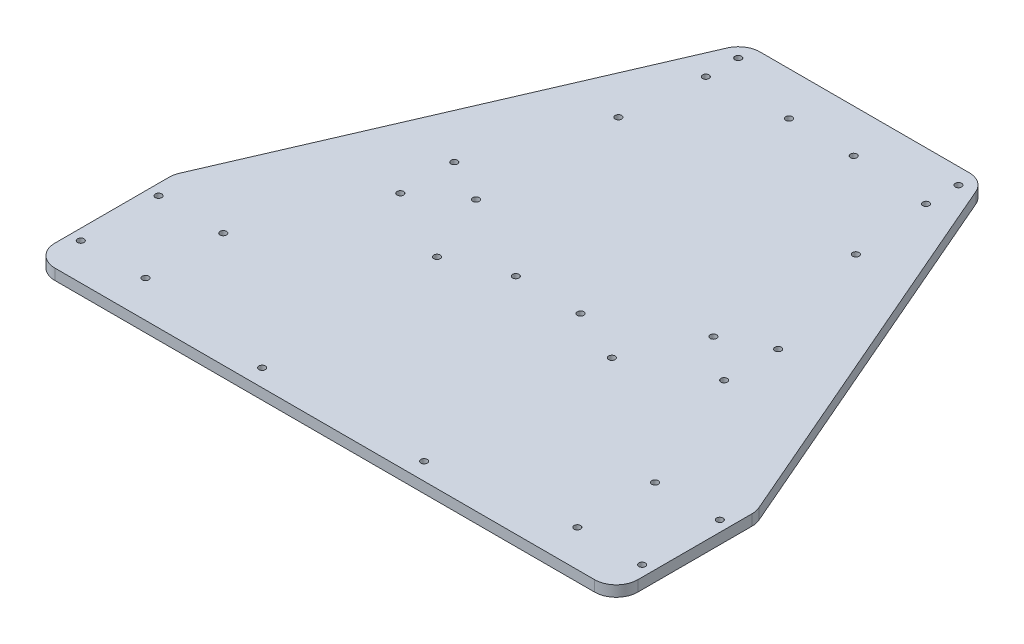
SolidWorks part; units mm, degrees
material "西洋杉"
ref_plane "正面" through (0, 0, 0) normal (0, 0, 1) x (1, 0, 0)
ref_plane "平面" through (0, 0, 0) normal (0, 1, 0) x (1, 0, 0)
ref_plane "右側面" through (0, 0, 0) normal (1, 0, 0) x (0, 0, -1)
sketch "ｽｹｯﾁ1" plane through (0, 0, 0) normal (0, 1, 0) x (1, 0, 0)
  line L0 (55, 125) -> (135, -60)
  line L1 (-135, -125) -> (135, -125)
  line L2 (-135, -125) -> (-135, 125)
  line L3 (-135, 125) -> (135, 125)
  line L4 (135, -125) -> (135, 125)
  line L5 (-135, -125) -> (135, 125) construction
  line L6 (-135, 125) -> (135, -125) construction
  line L7 (-55, 125) -> (-135, -60)
  point P0 (0, 0)
  dimension "D1" = 270
  dimension "D2" = 250
  dimension "D3" = 80
  dimension "D4" = 80
  dimension "D5" = 185
  dimension "D6" = 185
extrude "シャーシ形成" add sketch "ｽｹｯﾁ1" along normal blind 5 contours L3 L7 L2 L1 L4 L0
sketch "ｽｹｯﾁ2" plane through (0, 0, 0) normal (0, -1, 0) x (1, 0, 0)
  line L0 (130, 90) -> (130, 108)
  line L1 (-135, 90) -> (152.5185, 90)
  line L2 (-135, 125) -> (-135, 60) construction
  line L3 (-135, 125) -> (135, 125) construction
  line L4 (135, 125) -> (135, 60) construction
  line L5 (-130, 90) -> (-130, 72)
  line L6 (-130, 90) -> (-130, 108)
  line L7 (130, 90) -> (130, 72)
  circle A0 centre (-130, 90) radius 1.5
  circle A1 centre (130, 90) radius 1.5
  circle A2 centre (-130, 72) radius 1.5
  circle A3 centre (-130, 108) radius 1.5
  circle A4 centre (130, 72) radius 1.5
  circle A5 centre (130, 108) radius 1.5
  dimension "D4" = 3
  dimension "D5" = 3
  dimension "D10" = 3
  dimension "D11" = 3
  dimension "D12" = 3
  dimension "D13" = 3
  dimension "D1" = 35
  dimension "D2" = 5
  dimension "D3" = 5
  dimension "D6" = 18
  dimension "D7" = 18
  dimension "D8" = 18
  dimension "D9" = 18
extrude "外側モータマウンタ穴" cut sketch "ｽｹｯﾁ2" against normal through all contours A2 | A3 | A4 | A5
fillet "角ﾌｨﾚｯﾄ" radius 10 6 edges at (135, 2.5, 60) (135, 2.5, 125) (-135, 2.5, 125) (-135, 2.5, 60) (-55, 2.5, -125) (55, 2.5, -125)
sketch "ｽｹｯﾁ9" plane through (0, 0, 0) normal (0, -1, 0) x (1, 0, 0)
  line L0 (0, -125) -> (0, -105)
  line L1 (-48.4294, -125) -> (48.4294, -125) construction
  line L2 (0, -105) -> (15, -105)
  line L3 (15, -105) -> (-15, -105)
  circle A0 centre (15, -105) radius 1.5
  circle A1 centre (-15, -105) radius 1.5
  dimension "D4" = 3
  dimension "D5" = 3
  dimension "D1" = 20
  dimension "D2" = 15
  dimension "D3" = 30
extrude "キャスター穴" cut sketch "ｽｹｯﾁ9" against normal blind 5 contours A0 | A1
ref_plane "平面1" through (-134.1786, 5, 58.1004) normal (-0.3969, 0, 0.9179) x (0.9179, 0, 0.3969)
ref_plane "平面2" through (0, 5, 0) normal (0, -1, 0) x (-1, 0, 0)
sketch "ｽｹｯﾁ35" plane through (0, 0, 0) normal (0, -1, 0) x (1, 0, 0)
  line L0 (-48.4294, -125) -> (48.4294, -125) construction
  line L1 (0, -125) -> (50, -125)
  line L2 (0, -125) -> (0, 21.5)
  line L3 (0, 21.5) -> (50, 21.5)
  line L4 (50, -125) -> (50, 21.5)
  line L6 (0, -125) -> (-50, -125)
  line L7 (0, -125) -> (0, 21.5)
  line L8 (0, 21.5) -> (-50, 21.5)
  line L9 (-50, -125) -> (-50, 21.5)
  circle A1 centre (-15, 21.5) radius 1.5
  circle A2 centre (15, 21.5) radius 1.5
  dimension "D5" = 3
  dimension "D6" = 3
  dimension "D1" = 50
  dimension "D2" = 50
  dimension "D3" = 146.5
  dimension "D9" = 15
  dimension "D10" = 15
extrude "バッテリー固定棒の穴" cut sketch "ｽｹｯﾁ35" against normal blind 5
sketch "ｽｹｯﾁ38" plane through (0, 0, 0) normal (0, -1, 0) x (1, 0, 0)
  circle A0 centre (-100, 72) radius 1.5
  circle A1 centre (-100, 108) radius 1.5
  circle A2 centre (-130, 108) radius 1.5 construction
  circle A3 centre (-130, 72) radius 1.5 construction
  dimension "D3" = 3
  dimension "D4" = 3
  dimension "D6" = 30
  dimension "D8" = 36
  dimension "D5" = 30
  dimension "D7" = 0
extrude "内側モータマウンタ穴1" cut sketch "ｽｹｯﾁ38" against normal blind 5 contours A0 | A1
sketch "ｽｹｯﾁ39" plane through (0, 0, 0) normal (0, -1, 0) x (-1, 0, 0)
  circle A0 centre (-100, -72) radius 1.5
  circle A1 centre (-100, -108) radius 1.5
  circle A2 centre (-130, -108) radius 1.5 construction
  circle A3 centre (-130, -108) radius 1.5 construction
  circle A5 centre (-130, -72) radius 1.5 construction
  dimension "D1" = 3
  dimension "D2" = 3
  dimension "D5" = 0
  dimension "D6" = 0
  dimension "D3" = 30
  dimension "D4" = 30
extrude "内側モータマウンタ穴2" cut sketch "ｽｹｯﾁ39" against normal blind 5
sketch "ｽｹｯﾁ40" plane through (0, 0, 0) normal (0, -1, 0) x (1, 0, 0)
  line L0 (-48.4294, -125) -> (48.4294, -125) construction
  circle A0 centre (51, -117.5) radius 1.5
  circle A1 centre (-51, -117.5) radius 1.5
  circle A2 centre (51, -102.5) radius 1.5
  circle A3 centre (-51, -102.5) radius 1.5
  point P6 (0, -125)
  dimension "D1" = 3
  dimension "D2" = 3
  dimension "D3" = 102
  dimension "D6" = 3
  dimension "D8" = 3
  dimension "D4" = 7.5
  dimension "D5" = 51
  dimension "D7" = 15
  dimension "D9" = 15
extrude "カメラマウンタ穴" cut sketch "ｽｹｯﾁ40" against normal blind 5
sketch "ｽｹｯﾁ41" plane through (0, 0, 0) normal (0, -1, 0) x (1, 0, 0)
  line L0 (-125, 125) -> (125, 125) construction
  line L1 (135, 115) -> (135, 62.0696) construction
  line L2 (-125, 125) -> (125, 125) construction
  line L3 (-135, 115) -> (-135, 62.0696) construction
  circle A0 centre (75, 15) radius 1.5
  circle A1 centre (75, -10) radius 1.5
  circle A2 centre (-75, 15) radius 1.5
  circle A3 centre (-75, -10) radius 1.5
  dimension "D1" = 3
  dimension "D4" = 3
  dimension "D6" = 3
  dimension "D7" = 3
  dimension "D2" = 110
  dimension "D3" = 60
  dimension "D5" = 25
  dimension "D8" = 25
  dimension "D9" = 110
  dimension "D10" = 60
extrude "センサマウンタ穴" cut sketch "ｽｹｯﾁ41" against normal blind 5
sketch "ｽｹｯﾁ43" plane through (0, 0, 0) normal (0, -1, 0) x (1, 0, 0)
  line L0 (-135, 115) -> (-135, 62.0696) construction
  line L1 (-125, 125) -> (125, 125) construction
  line L2 (135, 115) -> (135, 62.0696) construction
  circle A0 centre (-55, 0) radius 1.5
  circle A1 centre (-55, -66) radius 1.5
  circle A2 centre (55, 0) radius 1.5
  circle A3 centre (55, -66) radius 1.5
  dimension "D1" = 3
  dimension "D4" = 3
  dimension "D6" = 3
  dimension "D9" = 3
  dimension "D2" = 80
  dimension "D3" = 125
  dimension "D5" = 66
  dimension "D7" = 125
  dimension "D8" = 80
  dimension "D10" = 66
extrude "電源ボードなどの穴" cut sketch "ｽｹｯﾁ43" against normal blind 5
sketch "ｽｹｯﾁ44" plane through (0, 0, 0) normal (0, -1, 0) x (1, 0, 0)
  line L2 (-125, 125) -> (125, 125) construction
  line L4 (-125, 125) -> (125, 125) construction
  line L6 (-135, 115) -> (-135, 62.0696) construction
  line L8 (135, 115) -> (135, 62.0696) construction
  circle A0 centre (-41, 32) radius 1.5
  circle A1 centre (40, 32) radius 1.5
  circle A2 centre (38, 117) radius 1.5
  circle A3 centre (-37, 117) radius 1.5
  dimension "D1" = 3
  dimension "D2" = 3
  dimension "D5" = 3
  dimension "D6" = 3
  dimension "D3" = 94
  dimension "D4" = 95
  dimension "D7" = 98
  dimension "D8" = 97
  dimension "D9" = 85
  dimension "D10" = 85
  dimension "D11" = 8
  dimension "D12" = 8
extrude "CPUタワー穴" cut sketch "ｽｹｯﾁ44" against normal blind 5
